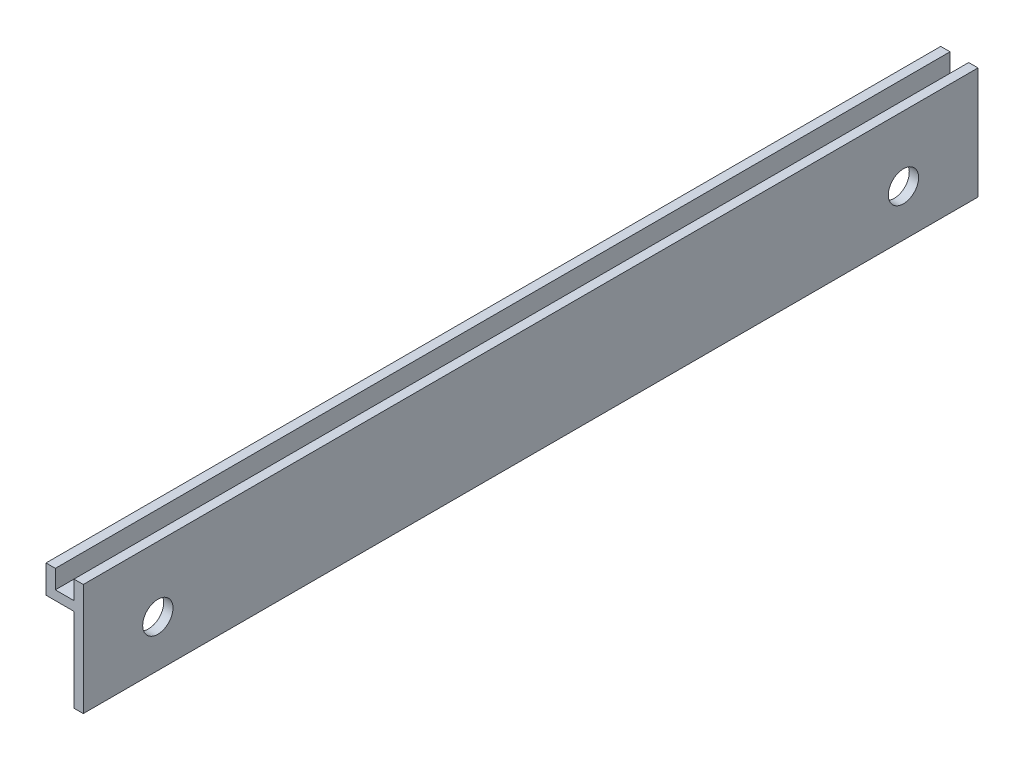
SolidWorks part; units mm, degrees
material "6061-T6 (SS)"
ref_plane "Front Plane" through (0, 0, 0) normal (0, 0, 1) x (1, 0, 0)
ref_plane "Top Plane" through (0, 0, 0) normal (0, 1, 0) x (1, 0, 0)
ref_plane "Right Plane" through (0, 0, 0) normal (1, 0, 0) x (0, 0, -1)
sketch "Sketch1" plane through (0, 0, 0) normal (0, 0, 1) x (1, 0, 0)
  line L1 (-6.35, 19.05) -> (-4.7625, 19.05)
  line L2 (-6.35, 19.05) -> (-6.35, 14.2875)
  line L3 (-1.5875, 0) -> (0, 0)
  line L4 (0, 19.05) -> (0, 0)
  line L5 (-1.5875, 14.2875) -> (-6.35, 14.2875)
  line L6 (-1.5875, 14.2875) -> (-1.5875, 0)
  line L7 (-4.7625, 19.05) -> (-4.7625, 15.875)
  line L11 (-4.7625, 15.875) -> (-1.5875, 15.875)
  line L12 (-1.5875, 15.875) -> (-1.5875, 19.05)
  line L13 (-1.5875, 19.05) -> (0, 19.05)
  point P5 (0, 0)
  dimension "D1" = 19.05
  dimension "D2" = 1.5875
  dimension "D3" = 3.175
  dimension "D4" = 1.5875
  dimension "D5" = 1.5875
  dimension "D6" = 15.875
extrude "Boss-Extrude1" add sketch "Sketch1" along normal blind 152.4
sketch "Sketch2" plane through (-1.5875, 0, 0) normal (-1, 0, 0) x (0, 0, 1)
  line L0 (152.4, 14.2875) -> (152.4, 0) construction
  line L1 (152.4, 14.2875) -> (0, 14.2875) construction
  circle A0 centre (12.7, 7.9375) radius 2.5797
  circle A1 centre (139.7, 7.9375) radius 2.5797
  dimension "D1" = 127
  dimension "D4" = 5.1594
  dimension "D2" = 12.7
  dimension "D3" = 6.35
extrude "Cut-Extrude1" cut sketch "Sketch2" against normal through all
